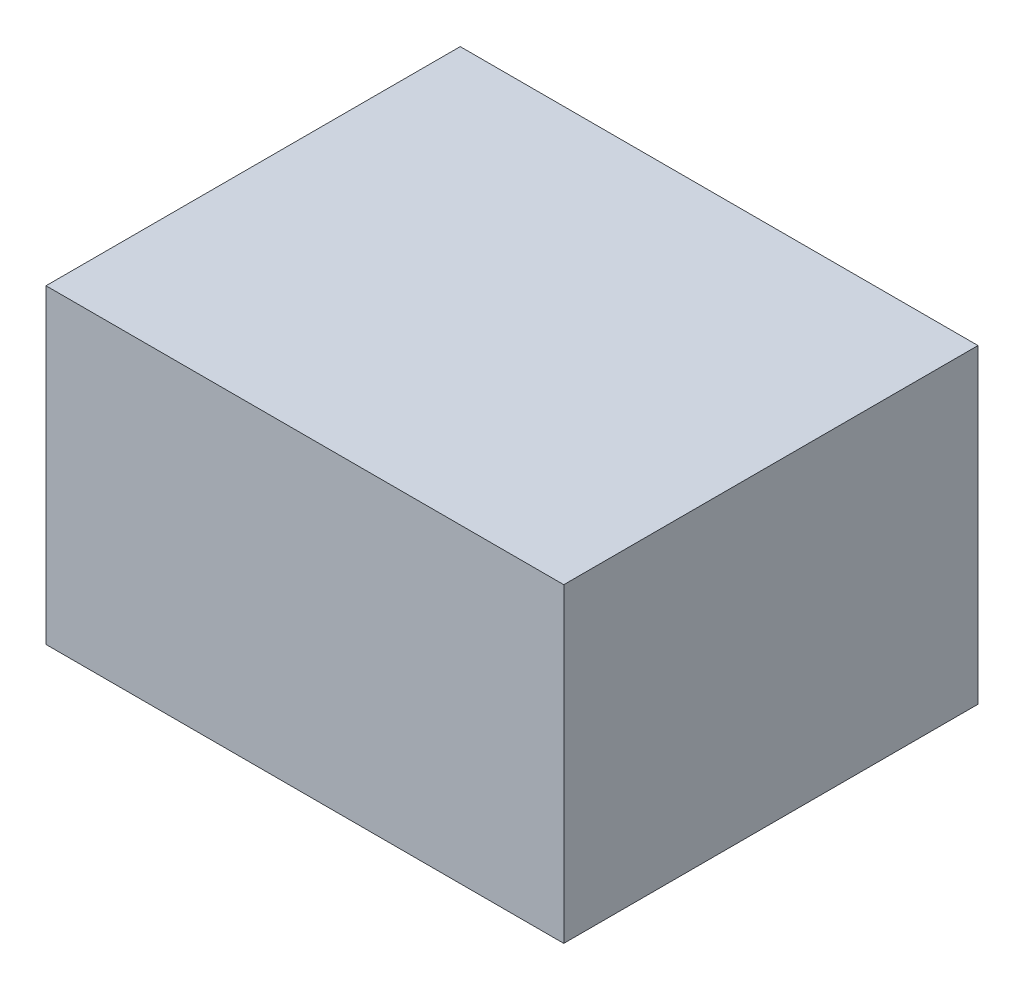
SolidWorks part; units mm, degrees
ref_plane "Front Plane" through (0, 0, 0) normal (0, 0, 1) x (1, 0, 0)
ref_plane "Top Plane" through (0, 0, 0) normal (0, 1, 0) x (1, 0, 0)
ref_plane "Right Plane" through (0, 0, 0) normal (1, 0, 0) x (0, 0, -1)
sketch "Sketch1" plane through (0, 0, 0) normal (0, 1, 0) x (1, 0, 0)
  line L1 (-127, -101.6) -> (127, -101.6)
  line L2 (-127, -101.6) -> (-127, 101.6)
  line L3 (-127, 101.6) -> (127, 101.6)
  line L4 (127, -101.6) -> (127, 101.6)
  line L5 (-127, -101.6) -> (127, 101.6) construction
  line L6 (-127, 101.6) -> (127, -101.6) construction
  point P0 (0, 0)
  dimension "D1" = 203.2
  dimension "D2" = 254
extrude "Boss-Extrude1" add sketch "Sketch1" along normal blind 152.4
